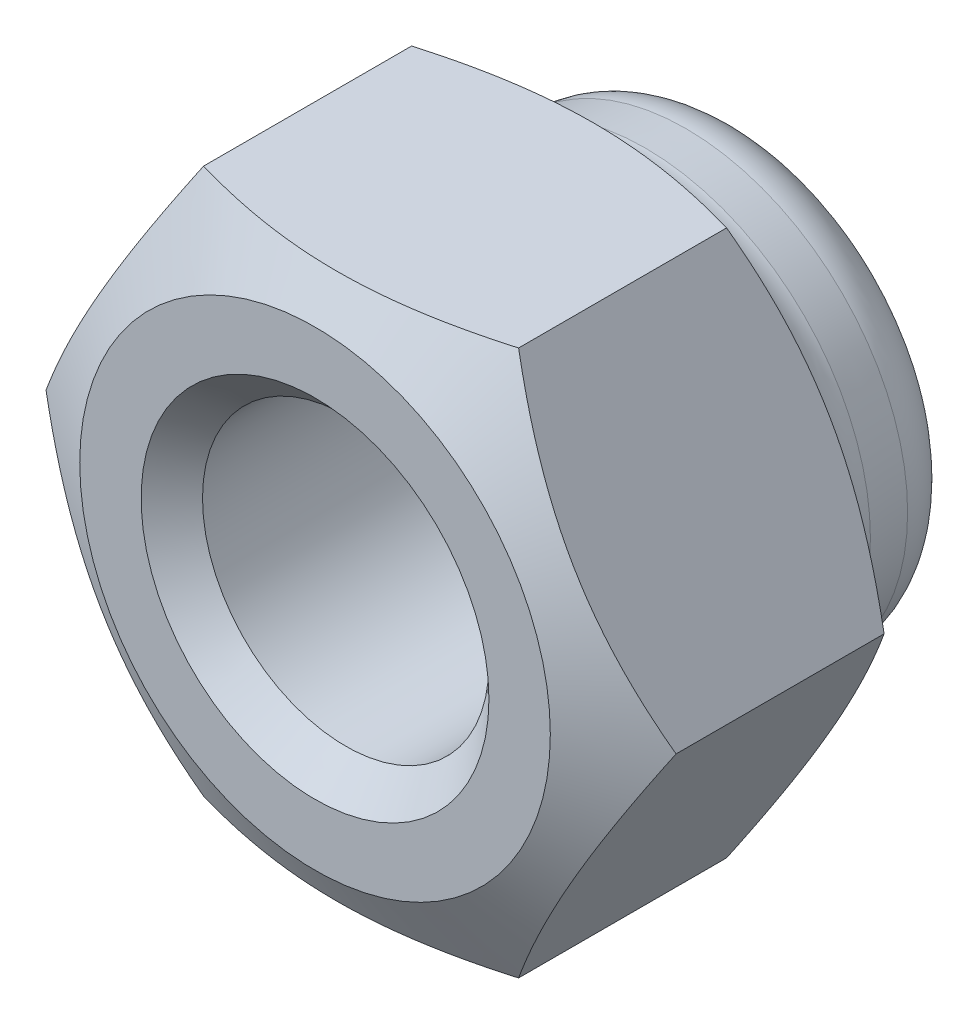
SolidWorks part; units mm, degrees
ref_plane "Front Plane" through (0, 0, 0) normal (0, 0, 1) x (1, 0, 0)
ref_plane "Top Plane" through (0, 0, 0) normal (0, 1, 0) x (1, 0, 0)
ref_plane "Right Plane" through (0, 0, 0) normal (1, 0, 0) x (0, 0, -1)
sketch "Sketch1" plane through (0, 0, 0) normal (0, 0, 1) x (1, 0, 0)
  line L0 (0, 0) -> (4.6188, 0) construction
  line L1 (4.6188, 0) -> (2.3094, 4)
  line L2 (2.3094, 4) -> (-2.3094, 4)
  line L3 (-2.3094, 4) -> (-4.6188, 0)
  line L4 (-4.6188, 0) -> (-2.3094, -4)
  line L5 (-2.3094, -4) -> (2.3094, -4)
  line L6 (2.3094, -4) -> (4.6188, 0)
  circle A0 centre (0, 0) radius 4 construction
  dimension "D1" = 8
extrude "Boss-Extrude1" add sketch "Sketch1" against normal blind 4.4
sketch "Sketch2" plane through (0, 0, 0) normal (1, 0, 0) x (0, 0, -1)
  line L0 (-11.9542, 0) -> (107.8579, 0) construction
  line L1 (4.4, 2) -> (6.0113, 2)
  line L5 (4.4, 3.45) -> (4.4, 2)
  line L6 (4.4, 0) -> (4.4, 4) construction
  line L7 (5.4387, 3.25) -> (4.841, 3.3023)
  line L10 (6.1613, 2.25) -> (6.0113, 2.25)
  line L11 (6.0113, 2) -> (6.0113, 2.25)
  line L14 (0, 0) -> (0, 4) construction
  arc A9 (6.1613, 2.25) -> (6.3, 2.3887) centre (6.1613, 2.3887) ccw
  arc A10 (5.4387, 3.25) -> (6.3, 2.3887) centre (5.4387, 2.3887) cw
  arc A11 (4.841, 3.3023) -> (4.4, 3.45) centre (4.841, 4.0345) cw
  dimension "D3" = 0.15
  dimension "D6" = 4.5
  dimension "D1" = 6.9
  dimension "D7" = 6.3
  dimension "D5" = 0.1387
  dimension "D9" = 0.6
  dimension "D2" = 6.5
  dimension "D4" = 4
  dimension "D8" = 5
revolve "Revolve1" add sketch "Sketch2" angle 360 about L0
sketch "Sketch3" plane through (0, 0, 0) normal (0, 1, 0) x (1, 0, 0)
  line L0 (0, 0) -> (0, 7.5743) construction
  line L1 (-3.45, 4.4) -> (-4.6188, 3.7252)
  line L2 (-3.45, 0) -> (-4.6188, 0.6748)
  line L3 (-4.6188, 3.7252) -> (-4.6188, 4.4)
  line L4 (-4.6188, 4.4) -> (-3.45, 4.4)
  line L11 (-4.6188, 4.4) -> (-4.6188, 0) construction
  line L16 (-4.6188, 0.6748) -> (-4.6188, 0)
  line L17 (-4.6188, 0) -> (-3.45, 0)
  line L18 (-2.3094, 0) -> (-4.6188, 0) construction
  dimension "D1" = 30
revolve "Cut-Revolve1" cut sketch "Sketch3" angle 360 about L0
sketch "Sketch4" plane through (0, 0, 0) normal (1, 0, 0) x (0, 0, -1)
  line L0 (-1.4124, 0) -> (7.5576, 0) construction
  line L1 (0, 2.55) -> (0.45, 2.1)
  line L3 (0.45, 2.1) -> (4.4, 2.1)
  line L5 (4.4, 2.1) -> (4.4, 0)
  line L7 (4.4, 0) -> (0, 0)
  line L8 (0, 0) -> (0, 2.55)
  dimension "D1" = 5.1
  dimension "D2" = 4.2
  dimension "D3" = 4.4
  dimension "D4" = 45
revolve "Cut-Revolve2" cut sketch "Sketch4" angle 360 about L0
cosmetic thread "Cosmetic Thread1" parameters "D2"=5
